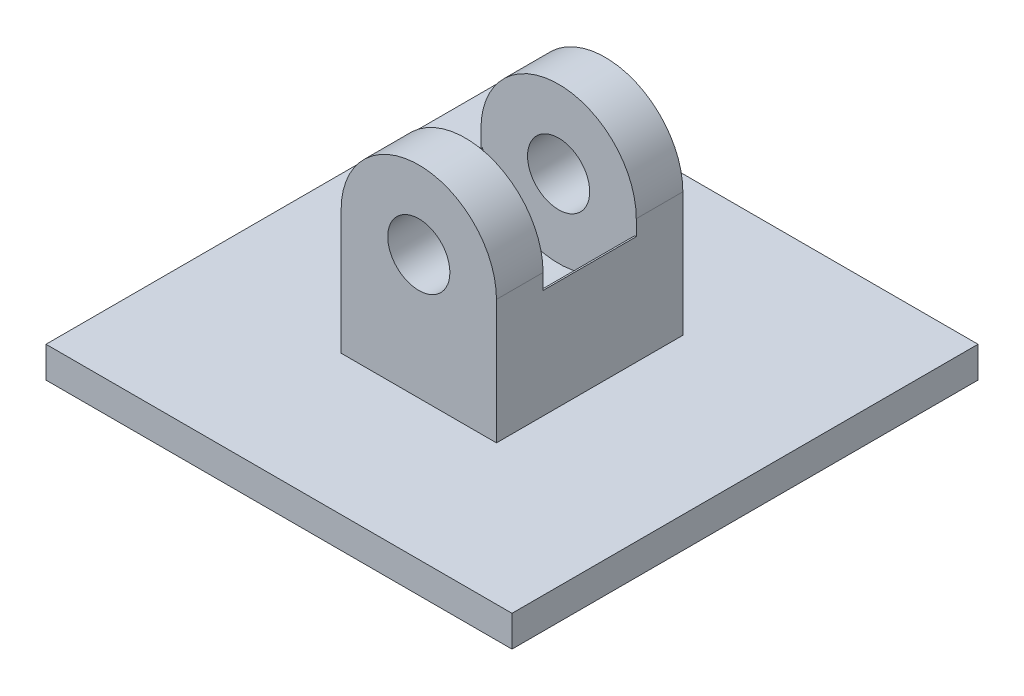
SolidWorks part; units mm, degrees
material "Acero al carbono no aleado"
ref_plane "Front Plane" through (0, 0, 0) normal (0, 0, 1) x (1, 0, 0)
ref_plane "Top Plane" through (0, 0, 0) normal (0, 1, 0) x (1, 0, 0)
ref_plane "Right Plane" through (0, 0, 0) normal (1, 0, 0) x (0, 0, -1)
sketch "Sketch1" plane through (0, 0, 0) normal (0, 1, 0) x (1, 0, 0)
  line L1 (75, -75) -> (-75, -75)
  line L2 (75, -75) -> (75, 75)
  line L3 (75, 75) -> (-75, 75)
  line L4 (-75, -75) -> (-75, 75)
  line L5 (75, -75) -> (-75, 75) construction
  line L6 (75, 75) -> (-75, -75) construction
  point P0 (0, 0)
  dimension "D1" = 150
  dimension "D2" = 150
extrude "Boss-Extrude1" add sketch "Sketch1" along normal blind 10
sketch "Sketch2" plane through (0, 10, 0) normal (0, 1, 0) x (1, 0, 0)
  line L1 (25, -30) -> (-25, -30)
  line L2 (25, -30) -> (25, 30)
  line L3 (25, 30) -> (-25, 30)
  line L4 (-25, -30) -> (-25, 30)
  line L5 (25, -30) -> (-25, 30) construction
  line L6 (25, 30) -> (-25, -30) construction
  point P0 (0, 0)
  dimension "D1" = 50
  dimension "D2" = 60
extrude "Boss-Extrude2" add sketch "Sketch2" along normal blind 40
sketch "Sketch3" plane through (0, 0, 30) normal (0, 0, 1) x (1, 0, 0)
  line L0 (-25, 50) -> (25, 50)
  arc A0 (25, 50) -> (-25, 50) centre (0, 50) ccw
extrude "Boss-Extrude3" add sketch "Sketch3" against normal up to surface (60 mm away) up to face at (0, 30, -30)
sketch "Sketch4" plane through (0, 0, 30) normal (0, 0, 1) x (1, 0, 0)
  line L0 (-25, 10) -> (25, 10) construction
  circle A0 centre (0, 50) radius 10
  dimension "D1" = 20
  dimension "D2" = 40
extrude "Cut-Extrude1" cut sketch "Sketch4" against normal up to surface (60 mm away) up to face at (0, 36.25, -30)
sketch "Sketch5" plane through (-25, 0, 0) normal (-1, 0, 0) x (0, 0, 1)
  line L5 (15, 45) -> (-15, 45)
  line L6 (15, 45) -> (15, 75)
  line L7 (15, 75) -> (-15, 75)
  line L8 (-15, 45) -> (-15, 75)
  line L9 (15, 45) -> (-15, 75) construction
  line L10 (15, 75) -> (-15, 45) construction
  line L12 (-30, 10) -> (30, 10) construction
  line L13 (30, 50) -> (30, 10) construction
  point P0 (0, 60)
  dimension "D1" = 30
  dimension "D2" = 50
  dimension "D3" = 30
  dimension "D4" = 30
extrude "Cut-Extrude2" cut sketch "Sketch5" against normal up to surface (50 mm away) up to face at (25, 30, 0)
sketch "Sketch6" plane through (0, 0, -15) normal (0, 0, 1) x (1, 0, 0)
  line L0 (0, 75) -> (0, 0) construction
  arc A0 (25, 50) -> (-25, 50) centre (0, 50) ccw construction
  circle A3 centre (0, 50) radius 25
  dimension "D1" = 50
extrude "Cut-Extrude3" cut sketch "Sketch6" along normal up to surface (30 mm away) up to face at (0, 53.3333, 15)
